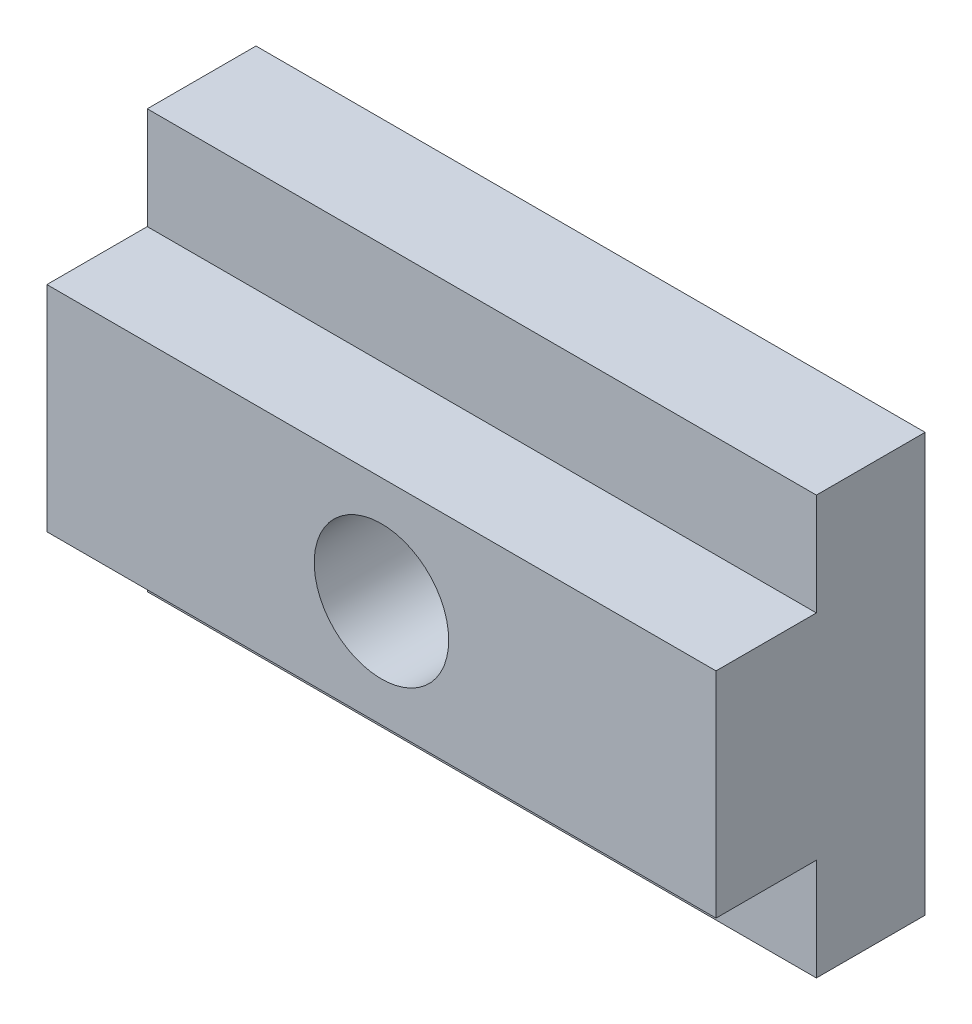
SolidWorks part; units mm, degrees
ref_plane "Front Plane" through (0, 0, 0) normal (0, 0, 1) x (1, 0, 0)
ref_plane "Top Plane" through (0, 0, 0) normal (0, 1, 0) x (1, 0, 0)
ref_plane "Right Plane" through (0, 0, 0) normal (1, 0, 0) x (0, 0, -1)
sketch "Sketch1" plane through (0, 0, 0) normal (0, 0, 1) x (1, 0, 0)
  line L1 (-12.7, 7.9375) -> (12.7, 7.9375)
  line L2 (-12.7, 7.9375) -> (-12.7, -7.9375)
  line L3 (-12.7, -7.9375) -> (12.7, -7.9375)
  line L4 (12.7, 7.9375) -> (12.7, -7.9375)
  line L5 (-12.7, 7.9375) -> (12.7, -7.9375) construction
  line L6 (-12.7, -7.9375) -> (12.7, 7.9375) construction
  point P0 (0, 0)
  dimension "D1" = 25.4
  dimension "D2" = 15.875
extrude "Boss-Extrude1" add sketch "Sketch1" along normal blind 7.9375
sketch "Sketch2" plane through (12.7, 0, 0) normal (1, 0, 0) x (0, 0, -1)
  line L0 (-4.1275, 4.064) -> (-4.1275, -4.064) construction
  line L1 (-7.9375, 7.9375) -> (-4.1275, 7.9375)
  line L2 (-7.9375, 7.9375) -> (-7.9375, 4.064)
  line L3 (-7.9375, 4.064) -> (-4.1275, 4.064)
  line L4 (-4.1275, 7.9375) -> (-4.1275, 4.064)
  line L5 (-7.9375, -7.9375) -> (-4.1275, -7.9375)
  line L6 (-7.9375, -7.9375) -> (-7.9375, -4.064)
  line L7 (-7.9375, -4.064) -> (-4.1275, -4.064)
  line L8 (-4.1275, -7.9375) -> (-4.1275, -4.064)
  line L9 (-4.1275, 0) -> (0, 0) construction
  dimension "D1" = 8.128
  dimension "D2" = 3.81
extrude "Cut-Extrude1" cut sketch "Sketch2" against normal up to next
hole_wizard "1/4-20 Tapped Hole1" positions "Sketch4" profile "Sketch3" tap size "1/4-20" standard "ANSI Inch"
sketch "Sketch4" plane through (0, 0, 7.9375) normal (0, 0, 1) x (1, 0, 0)
  point P0 (0, 0)
sketch "Sketch3" plane through (0, 0, 7.9375) normal (1, 0, 0) x (0, -1, 0)
  line L0 (0, 0) -> (0, 18.0438)
  line L1 (0, 18.0438) -> (2.5527, 16.51)
  line L2 (2.5527, 16.51) -> (2.5527, 0)
  line L5 (2.5527, 0) -> (0, 0)
  line L10 (0, 18.0438) -> (-2.5527, 16.51) construction
  line L11 (0, -6.35) -> (0, 107.95) construction
  dimension "Tap Drill Dia." = 5.1054
  dimension "Tap Drill Depth" = 16.51
  dimension "Drill Angle" = 118
